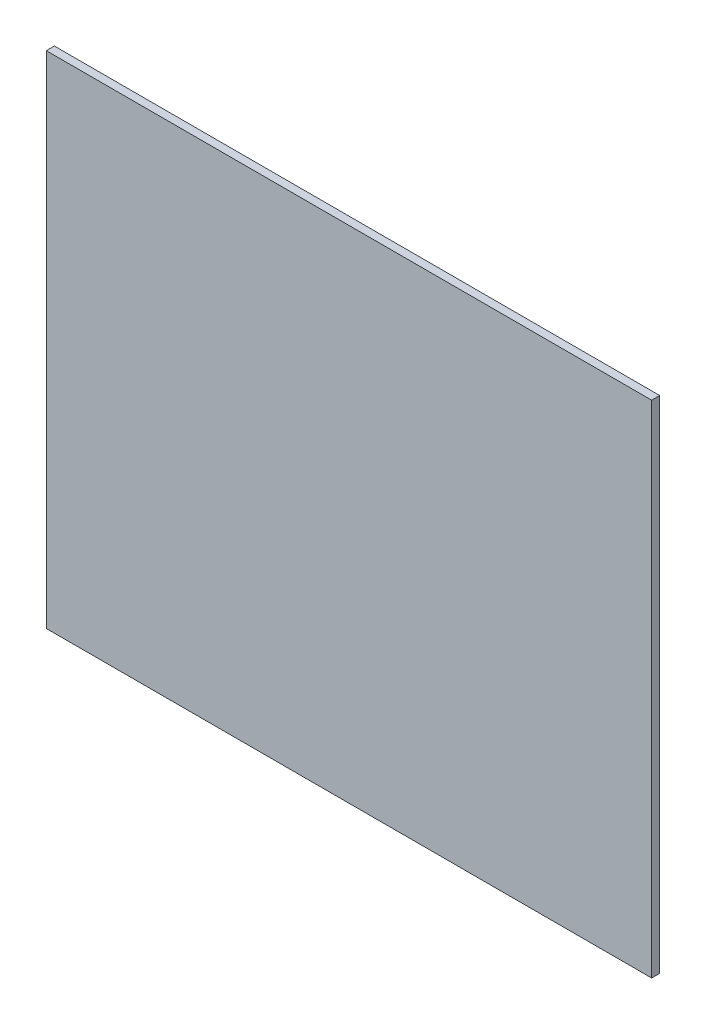
SolidWorks part; units mm, degrees
ref_plane "Plan de face" through (0, 0, 0) normal (0, 0, 1) x (1, 0, 0)
ref_plane "Plan de dessus" through (0, 0, 0) normal (0, 1, 0) x (1, 0, 0)
ref_plane "Plan de droite" through (0, 0, 0) normal (1, 0, 0) x (0, 0, -1)
sketch "Esquisse1" plane through (0, 0, 0) normal (0, 0, 1) x (1, 0, 0)
  line L1 (0, 0) -> (-375, 0)
  line L2 (0, 0) -> (0, 310)
  line L3 (0, 310) -> (-375, 310)
  line L4 (-375, 0) -> (-375, 310)
  dimension "D1" = 375
  dimension "D2" = 310
extrude "Boss.-Extru.1" add sketch "Esquisse1" along normal blind 5
